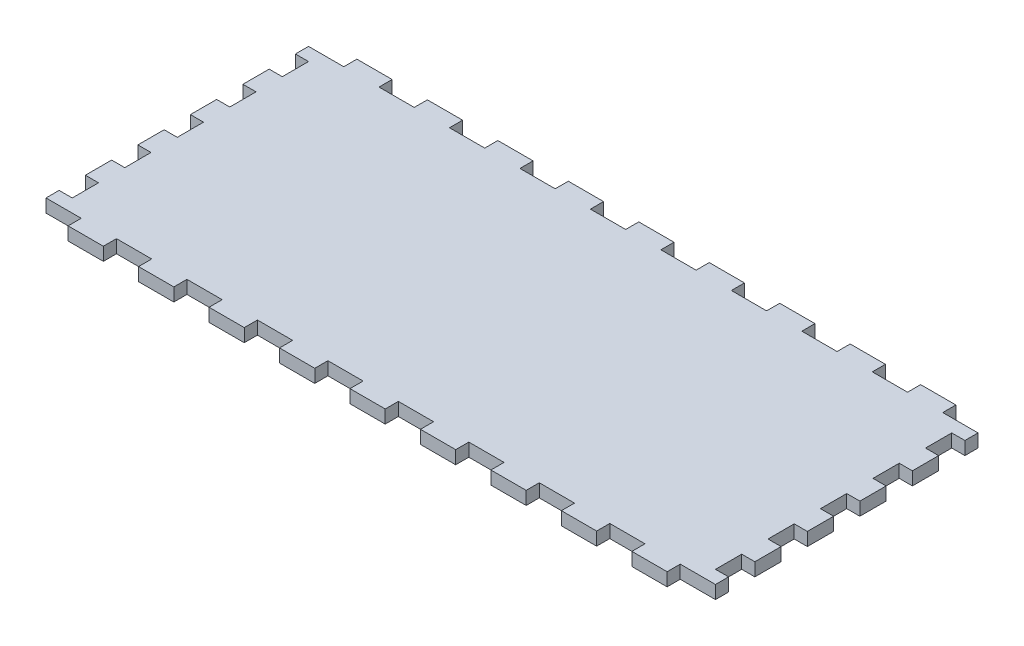
SolidWorks part; units mm, degrees
material "Acrylic (Medium-high impact)"
ref_plane "Front Plane" through (0, 0, 0) normal (0, 0, 1) x (1, 0, 0)
ref_plane "Top Plane" through (0, 0, 0) normal (0, 1, 0) x (1, 0, 0)
ref_plane "Right Plane" through (0, 0, 0) normal (1, 0, 0) x (0, 0, -1)
sketch "Sketch1" plane through (0, 0, 0) normal (0, 1, 0) x (1, 0, 0)
  line L1 (-161.925, 69.85) -> (161.925, 69.85)
  line L2 (-161.925, 69.85) -> (-161.925, -69.85)
  line L3 (-161.925, -69.85) -> (161.925, -69.85)
  line L4 (161.925, 69.85) -> (161.925, -69.85)
  point P4 (-161.925, 0)
  point P6 (0, 69.85)
  dimension "D1" = 139.7
  dimension "D2" = 323.85
extrude "Boss-Extrude1" add sketch "Sketch1" along normal blind 6.35
sketch "Sketch2" plane through (0, 6.35, 0) normal (0, 1, 0) x (1, 0, 0)
  line L0 (161.925, -69.85) -> (161.925, 69.85) construction
  line L1 (-161.925, 69.85) -> (161.925, 69.85)
  line L2 (-161.925, 69.85) -> (-161.925, -69.85)
  line L3 (-161.925, -69.85) -> (161.925, -69.85)
  line L4 (161.925, 69.85) -> (161.925, -69.85)
  line L5 (-161.925, -69.85) -> (161.925, -69.85) construction
  line L7 (-155.575, 63.5) -> (155.575, 63.5)
  line L8 (-155.575, 63.5) -> (-155.575, -63.5)
  line L9 (-155.575, -63.5) -> (155.575, -63.5)
  line L10 (155.575, 63.5) -> (155.575, -63.5)
  point P7 (-155.575, 0)
  point P14 (-161.925, 0)
  point P15 (0, -63.5)
  point P16 (0, -69.85)
  point P17 (155.575, 0)
  point P18 (161.925, 0)
  dimension "D1" = 6.35
  dimension "D2" = 6.35
extrude "Boss-Extrude2" add sketch "Sketch2" along normal blind 298.45
sketch "Sketch3" plane through (0, 0, 69.85) normal (0, 0, 1) x (1, 0, 0)
  line L0 (-50.673, 304.8) -> (-50.673, 0) construction
  line L2 (-155.575, 6.35) -> (155.575, 6.35) construction
  line L4 (-53.975, 283.21) -> (-53.975, 6.35)
  line L5 (-53.975, 6.35) -> (-47.371, 6.35)
  line L6 (-47.371, 292.354) -> (-47.371, 6.35)
  line L7 (-47.371, 292.354) -> (-66.929, 292.354)
  line L9 (-56.515, 285.75) -> (-66.929, 285.75)
  line L10 (-66.929, 292.354) -> (-66.929, 285.75)
  line L11 (-47.371, 101.6) -> (-34.671, 101.6) construction
  line L12 (-161.925, 0) -> (161.925, 0) construction
  line L13 (-37.846, 88.9) -> (-37.846, 101.6) construction
  line L14 (-41.021, 88.9) -> (-34.671, 88.9)
  line L15 (-41.021, 88.9) -> (-41.021, 71.9667)
  line L16 (-41.021, 71.9667) -> (-34.671, 71.9667)
  line L17 (-34.671, 88.9) -> (-34.671, 71.9667)
  line L18 (-41.021, 42.3333) -> (-34.671, 42.3333)
  line L19 (-41.021, 42.3333) -> (-41.021, 59.2667)
  line L20 (-41.021, 59.2667) -> (-34.671, 59.2667)
  line L21 (-34.671, 42.3333) -> (-34.671, 59.2667)
  line L26 (-41.021, 29.6333) -> (-34.671, 29.6333)
  line L27 (-41.021, 29.6333) -> (-41.021, 12.7)
  line L28 (-41.021, 12.7) -> (-34.671, 12.7)
  line L29 (-34.671, 29.6333) -> (-34.671, 12.7)
  line L30 (-37.846, 59.2667) -> (-37.846, 71.9667) construction
  line L31 (-37.846, 29.6333) -> (-37.846, 42.3333) construction
  line L32 (-37.846, 12.7) -> (-37.846, 0) construction
  line L33 (-161.925, 304.8) -> (161.925, 304.8) construction
  line L34 (-155.575, 304.8) -> (-155.575, 6.35) construction
  arc A0 (-53.975, 283.21) -> (-56.515, 285.75) centre (-56.515, 283.21) ccw
  point P5 (-50.673, 6.35)
  dimension "D5" = 2.54
  dimension "D1" = 6.604
  dimension "D2" = 12.954
  dimension "D3" = 6.604
  dimension "D4" = 286.004
  dimension "D6" = 101.6
  dimension "D7" = 12.7
  dimension "D8" = 12.7
  dimension "D9" = 6.35
  dimension "D10" = 101.6
extrude "Door Slot" cut sketch "Sketch3" against normal blind 12.7
sketch "Sketch4" plane through (0, 0, -63.5) normal (0, 0, 1) x (1, 0, 0)
  line L0 (-161.925, 304.8) -> (161.925, 304.8) construction
  line L1 (-73.279, 304.8) -> (-66.929, 304.8)
  line L2 (-73.279, 304.8) -> (-73.279, 6.35)
  line L3 (-73.279, 6.35) -> (-66.929, 6.35)
  line L4 (-66.929, 304.8) -> (-66.929, 6.35)
  line L5 (-44.196, 263.525) -> (-44.196, 247.65) construction
  line L6 (-66.929, 292.354) -> (-66.929, 285.75) construction
  line L7 (-47.371, 304.8) -> (-41.021, 304.8)
  line L8 (-47.371, 304.8) -> (-47.371, 6.35)
  line L9 (-47.371, 6.35) -> (-41.021, 6.35)
  line L10 (-41.021, 304.8) -> (-41.021, 6.35)
  line L11 (155.575, 6.35) -> (-155.575, 6.35) construction
  line L12 (-47.371, 6.35) -> (-47.371, 292.354) construction
  line L13 (-66.929, 304.8) -> (-73.279, 304.8)
  line L14 (-66.929, 304.8) -> (-66.929, 292.1)
  line L15 (-66.929, 292.1) -> (-73.279, 292.1)
  line L16 (-73.279, 304.8) -> (-73.279, 292.1)
  line L17 (-66.929, 276.225) -> (-73.279, 276.225)
  line L18 (-66.929, 276.225) -> (-66.929, 263.525)
  line L19 (-66.929, 263.525) -> (-73.279, 263.525)
  line L20 (-73.279, 276.225) -> (-73.279, 263.525)
  line L21 (-73.279, 6.35) -> (-66.929, 6.35)
  line L22 (-73.279, 6.35) -> (-73.279, 19.05)
  line L23 (-73.279, 19.05) -> (-66.929, 19.05)
  line L24 (-66.929, 6.35) -> (-66.929, 19.05)
  line L25 (-73.279, 34.925) -> (-66.929, 34.925)
  line L26 (-73.279, 34.925) -> (-73.279, 47.625)
  line L27 (-73.279, 47.625) -> (-66.929, 47.625)
  line L28 (-66.929, 34.925) -> (-66.929, 47.625)
  line L29 (-73.279, 92.075) -> (-66.929, 92.075)
  line L30 (-73.279, 92.075) -> (-73.279, 104.775)
  line L31 (-73.279, 104.775) -> (-66.929, 104.775)
  line L32 (-66.929, 92.075) -> (-66.929, 104.775)
  line L33 (-73.279, 149.225) -> (-66.929, 149.225)
  line L34 (-73.279, 149.225) -> (-73.279, 161.925)
  line L35 (-73.279, 161.925) -> (-66.929, 161.925)
  line L36 (-66.929, 149.225) -> (-66.929, 161.925)
  line L37 (-73.279, 177.8) -> (-66.929, 177.8)
  line L38 (-73.279, 177.8) -> (-73.279, 190.5)
  line L39 (-73.279, 190.5) -> (-66.929, 190.5)
  line L40 (-66.929, 177.8) -> (-66.929, 190.5)
  line L41 (-73.279, 206.375) -> (-66.929, 206.375)
  line L42 (-73.279, 206.375) -> (-73.279, 219.075)
  line L43 (-73.279, 219.075) -> (-66.929, 219.075)
  line L44 (-66.929, 206.375) -> (-66.929, 219.075)
  line L45 (-73.279, 234.95) -> (-66.929, 234.95)
  line L46 (-73.279, 234.95) -> (-73.279, 247.65)
  line L47 (-73.279, 247.65) -> (-66.929, 247.65)
  line L48 (-66.929, 234.95) -> (-66.929, 247.65)
  line L49 (-66.929, 133.35) -> (-73.279, 133.35)
  line L50 (-66.929, 133.35) -> (-66.929, 120.65)
  line L51 (-66.929, 120.65) -> (-73.279, 120.65)
  line L52 (-73.279, 133.35) -> (-73.279, 120.65)
  line L53 (-66.929, 76.2) -> (-73.279, 76.2)
  line L54 (-66.929, 76.2) -> (-66.929, 63.5)
  line L55 (-66.929, 63.5) -> (-73.279, 63.5)
  line L56 (-73.279, 76.2) -> (-73.279, 63.5)
  line L57 (-70.104, 304.8) -> (-70.104, 292.1) construction
  line L58 (-70.104, 292.1) -> (-70.104, 276.225) construction
  line L59 (-70.104, 276.225) -> (-70.104, 263.525) construction
  line L60 (-70.104, 247.65) -> (-70.104, 234.95) construction
  line L61 (-70.104, 234.95) -> (-70.104, 219.075) construction
  line L62 (-70.104, 219.075) -> (-70.104, 206.375) construction
  line L63 (-70.104, 206.375) -> (-70.104, 190.5) construction
  line L64 (-70.104, 190.5) -> (-70.104, 177.8) construction
  line L65 (-70.104, 177.8) -> (-70.104, 161.925) construction
  line L66 (-70.104, 161.925) -> (-70.104, 149.225) construction
  line L67 (-70.104, 133.35) -> (-70.104, 120.65) construction
  line L68 (-70.104, 120.65) -> (-70.104, 104.775) construction
  line L69 (-70.104, 104.775) -> (-70.104, 92.075) construction
  line L70 (-70.104, 92.075) -> (-70.104, 76.2) construction
  line L71 (-70.104, 76.2) -> (-70.104, 63.5) construction
  line L72 (-70.104, 63.5) -> (-70.104, 47.625) construction
  line L73 (-70.104, 47.625) -> (-70.104, 34.925) construction
  line L74 (-70.104, 34.925) -> (-70.104, 19.05) construction
  line L75 (-70.104, 19.05) -> (-70.104, 6.35) construction
  line L76 (-70.104, 149.225) -> (-70.104, 133.35) construction
  line L77 (-70.104, 263.525) -> (-70.104, 247.65) construction
  line L78 (-57.15, 304.8) -> (-57.15, 0) construction
  line L79 (161.925, 304.8) -> (-161.925, 304.8) construction
  line L80 (161.925, 0) -> (-161.925, 0) construction
  line L81 (-57.15, 8.3493) -> (-47.371, 8.3493) construction
  line L82 (-57.15, 8.3493) -> (-66.929, 8.3493) construction
  line L83 (-44.196, 149.225) -> (-44.196, 133.35) construction
  line L84 (-44.196, 19.05) -> (-44.196, 6.35) construction
  line L85 (-44.196, 34.925) -> (-44.196, 19.05) construction
  line L86 (-44.196, 47.625) -> (-44.196, 34.925) construction
  line L87 (-44.196, 63.5) -> (-44.196, 47.625) construction
  line L88 (-44.196, 76.2) -> (-44.196, 63.5) construction
  line L89 (-44.196, 92.075) -> (-44.196, 76.2) construction
  line L90 (-44.196, 104.775) -> (-44.196, 92.075) construction
  line L91 (-44.196, 120.65) -> (-44.196, 104.775) construction
  line L92 (-44.196, 133.35) -> (-44.196, 120.65) construction
  line L93 (-44.196, 161.925) -> (-44.196, 149.225) construction
  line L94 (-44.196, 177.8) -> (-44.196, 161.925) construction
  line L95 (-44.196, 190.5) -> (-44.196, 177.8) construction
  line L96 (-44.196, 206.375) -> (-44.196, 190.5) construction
  line L97 (-44.196, 219.075) -> (-44.196, 206.375) construction
  line L98 (-44.196, 234.95) -> (-44.196, 219.075) construction
  line L99 (-44.196, 247.65) -> (-44.196, 234.95) construction
  line L100 (-44.196, 276.225) -> (-44.196, 263.525) construction
  line L101 (-44.196, 292.1) -> (-44.196, 276.225) construction
  line L102 (-44.196, 304.8) -> (-44.196, 292.1) construction
  line L103 (-41.021, 76.2) -> (-41.021, 63.5)
  line L104 (-47.371, 63.5) -> (-41.021, 63.5)
  line L105 (-47.371, 76.2) -> (-47.371, 63.5)
  line L106 (-47.371, 76.2) -> (-41.021, 76.2)
  line L107 (-41.021, 133.35) -> (-41.021, 120.65)
  line L108 (-47.371, 120.65) -> (-41.021, 120.65)
  line L109 (-47.371, 133.35) -> (-47.371, 120.65)
  line L110 (-47.371, 133.35) -> (-41.021, 133.35)
  line L111 (-47.371, 234.95) -> (-47.371, 247.65)
  line L112 (-41.021, 247.65) -> (-47.371, 247.65)
  line L113 (-41.021, 234.95) -> (-41.021, 247.65)
  line L114 (-41.021, 234.95) -> (-47.371, 234.95)
  line L115 (-47.371, 206.375) -> (-47.371, 219.075)
  line L116 (-41.021, 219.075) -> (-47.371, 219.075)
  line L117 (-41.021, 206.375) -> (-41.021, 219.075)
  line L118 (-41.021, 206.375) -> (-47.371, 206.375)
  line L119 (-47.371, 177.8) -> (-47.371, 190.5)
  line L120 (-41.021, 190.5) -> (-47.371, 190.5)
  line L121 (-41.021, 177.8) -> (-41.021, 190.5)
  line L122 (-41.021, 177.8) -> (-47.371, 177.8)
  line L123 (-47.371, 149.225) -> (-47.371, 161.925)
  line L124 (-41.021, 161.925) -> (-47.371, 161.925)
  line L125 (-41.021, 149.225) -> (-41.021, 161.925)
  line L126 (-41.021, 149.225) -> (-47.371, 149.225)
  line L127 (-47.371, 92.075) -> (-47.371, 104.775)
  line L128 (-41.021, 104.775) -> (-47.371, 104.775)
  line L129 (-41.021, 92.075) -> (-41.021, 104.775)
  line L130 (-41.021, 92.075) -> (-47.371, 92.075)
  line L131 (-47.371, 34.925) -> (-47.371, 47.625)
  line L132 (-41.021, 47.625) -> (-47.371, 47.625)
  line L133 (-41.021, 34.925) -> (-41.021, 47.625)
  line L134 (-41.021, 34.925) -> (-47.371, 34.925)
  line L135 (-47.371, 6.35) -> (-47.371, 19.05)
  line L136 (-41.021, 19.05) -> (-47.371, 19.05)
  line L137 (-41.021, 6.35) -> (-41.021, 19.05)
  line L138 (-41.021, 6.35) -> (-47.371, 6.35)
  line L139 (-41.021, 276.225) -> (-41.021, 263.525)
  line L140 (-47.371, 263.525) -> (-41.021, 263.525)
  line L141 (-47.371, 276.225) -> (-47.371, 263.525)
  line L142 (-47.371, 276.225) -> (-41.021, 276.225)
  line L143 (-41.021, 304.8) -> (-41.021, 292.1)
  line L144 (-47.371, 292.1) -> (-41.021, 292.1)
  line L145 (-47.371, 304.8) -> (-47.371, 292.1)
  line L146 (-47.371, 304.8) -> (-41.021, 304.8)
  line L147 (-47.371, 304.8) -> (-47.371, 6.35)
  line L148 (-41.021, 6.35) -> (-47.371, 6.35)
  line L149 (-41.021, 304.8) -> (-41.021, 6.35)
  line L150 (-41.021, 304.8) -> (-47.371, 304.8)
  point P14 (-66.929, 289.052)
  dimension "D1" = 6.35
  dimension "D2" = 12.7
extrude "Door Guide Holes" cut sketch "Sketch4" against normal up to next (6.35 mm away) contours L17 L4 L15 L2 | L2 L47 L4 L19 | L45 L2 L43 L4 | L41 L2 L39 L4 | L37 L2 L35 L4 | L49 L4 L33 L2 | L4 L51 L2 L31 | L53 L4 L29 L2 | L4 L55 L2 L27 | L25 L2 L23 L4
ref_plane "Plane1" through (-57.15, 0, 0) normal (-1, 0, 0) x (0, 0, 1)
mirror "Mirror1" about plane through (-57.15, 0, 0) normal (-1, 0, 0) of "Door Guide Holes"
sketch "Lever Holes" plane through (0, 0, 69.85) normal (0, 0, 1) x (1, 0, 0)
  line L0 (49.276, 31.75) -> (58.928, 31.75)
  line L1 (49.276, 31.75) -> (49.276, 25.4)
  line L2 (49.276, 25.4) -> (58.928, 25.4)
  line L3 (58.928, 31.75) -> (58.928, 25.4)
  line L4 (36.1315, 19.05) -> (42.4815, 19.05)
  line L5 (36.1315, 19.05) -> (36.1315, 12.7)
  line L6 (36.1315, 12.7) -> (42.4815, 12.7)
  line L7 (42.4815, 19.05) -> (42.4815, 12.7)
  line L8 (65.7225, 19.05) -> (72.0725, 19.05)
  line L9 (65.7225, 19.05) -> (65.7225, 12.7)
  line L10 (65.7225, 12.7) -> (72.0725, 12.7)
  line L11 (72.0725, 19.05) -> (72.0725, 12.7)
  line L12 (42.4815, 15.875) -> (65.7225, 15.875) construction
  line L13 (-161.925, 0) -> (161.925, 0) construction
  line L14 (-47.371, 6.35) -> (155.575, 6.35) construction
  line L15 (155.575, 6.35) -> (-155.575, 6.35) construction
  point P12 (54.102, 15.875)
  point P13 (54.102, 25.4)
  point P24 (54.102, 6.35)
  dimension "D1" = 9.652
  dimension "D2" = 6.35
  dimension "D3" = 6.35
  dimension "D4" = 6.35
  dimension "D5" = 23.241
  dimension "D6" = 25.4
  dimension "D7" = 12.7
extrude "Cut-Extrude1" cut sketch "Lever Holes" against normal through all
sketch "Sketch7" plane through (161.925, 0, 0) normal (1, 0, 0) x (0, 0, -1)
  line L0 (-37.211, 92.583) -> (37.211, 92.583)
  line L1 (-37.211, 92.583) -> (-37.211, 18.161)
  line L2 (-37.211, 18.161) -> (37.211, 18.161)
  line L3 (37.211, 92.583) -> (37.211, 18.161)
  line L4 (-69.85, 0) -> (69.85, 0) construction
  circle A0 centre (0, 55.372) radius 26.9875
  circle A1 centre (-37.211, 92.583) radius 3.175
  circle A2 centre (37.211, 92.583) radius 3.175
  circle A3 centre (-37.211, 18.161) radius 3.175
  circle A4 centre (37.211, 18.161) radius 3.175
  point P9 (0, 18.161)
  point P10 (-37.211, 55.372)
  dimension "D3" = 53.975
  dimension "D4" = 6.35
  dimension "D1" = 74.422
  dimension "D2" = 55.372
extrude "Cut-Extrude2" cut sketch "Sketch7" against normal up to next contours A0 | L0 A1 L1 | L1 A1 L0 | L3 A2 L0 | L0 A2 L3 | L2 A3 L1 | L1 A3 L2 | L2 A4 L3 | L3 A4 L2
sketch "Sketch8" plane through (-161.925, 0, 0) normal (-1, 0, 0) x (0, 0, 1)
  line L0 (-69.85, 0) -> (69.85, 0) construction
  circle A0 centre (0, 19.05) radius 3.175
  point P6 (0, 0)
  dimension "D1" = 6.35
  dimension "D2" = 19.05
extrude "Cut-Extrude3" cut sketch "Sketch8" against normal up to next
sketch "Sketch10" plane through (0, 0, 0) normal (0, -1, 0) x (1, 0, 0)
  line L0 (-155.575, 63.5) -> (155.575, 63.5) construction
  line L1 (-161.925, 69.85) -> (-144.8803, 69.85)
  line L2 (-161.925, 69.85) -> (-161.925, 63.5)
  line L3 (-161.925, 63.5) -> (-144.8803, 63.5)
  line L4 (-144.8803, 69.85) -> (-144.8803, 63.5)
  line L5 (-144.8803, 69.85) -> (-127.8355, 69.85)
  line L6 (-144.8803, 69.85) -> (-144.8803, 63.5)
  line L7 (-144.8803, 63.5) -> (-127.8355, 63.5)
  line L8 (-127.8355, 69.85) -> (-127.8355, 63.5)
  line L9 (-127.8355, 69.85) -> (-110.7908, 69.85)
  line L10 (-127.8355, 69.85) -> (-127.8355, 63.5)
  line L11 (-127.8355, 63.5) -> (-110.7908, 63.5)
  line L12 (-110.7908, 69.85) -> (-110.7908, 63.5)
  line L13 (-110.7908, 69.85) -> (-93.7461, 69.85)
  line L14 (-110.7908, 69.85) -> (-110.7908, 63.5)
  line L15 (-110.7908, 63.5) -> (-93.7461, 63.5)
  line L16 (-93.7461, 69.85) -> (-93.7461, 63.5)
  line L17 (-161.925, 69.85) -> (161.925, 69.85) construction
  line L18 (-66.929, 63.5) -> (-47.371, 63.5) construction
  line L19 (-93.7461, 69.85) -> (-76.7013, 69.85)
  line L20 (-93.7461, 69.85) -> (-93.7461, 63.5)
  line L21 (-93.7461, 63.5) -> (-76.7013, 63.5)
  line L22 (-76.7013, 69.85) -> (-76.7013, 63.5)
  line L23 (-76.7013, 69.85) -> (-59.6566, 69.85)
  line L24 (-76.7013, 69.85) -> (-76.7013, 63.5)
  line L25 (-76.7013, 63.5) -> (-59.6566, 63.5)
  line L26 (-59.6566, 69.85) -> (-59.6566, 63.5)
  line L27 (-59.6566, 69.85) -> (-42.6118, 69.85)
  line L28 (-59.6566, 69.85) -> (-59.6566, 63.5)
  line L29 (-59.6566, 63.5) -> (-42.6118, 63.5)
  line L30 (-42.6118, 69.85) -> (-42.6118, 63.5)
  line L31 (-42.6118, 69.85) -> (-25.5671, 69.85)
  line L32 (-42.6118, 69.85) -> (-42.6118, 63.5)
  line L33 (-42.6118, 63.5) -> (-25.5671, 63.5)
  line L34 (-25.5671, 69.85) -> (-25.5671, 63.5)
  line L36 (-25.5671, 69.85) -> (-8.5224, 69.85)
  line L37 (-25.5671, 69.85) -> (-25.5671, 63.5)
  line L38 (-25.5671, 63.5) -> (-8.5224, 63.5)
  line L39 (-8.5224, 69.85) -> (-8.5224, 63.5)
  line L40 (-8.5224, 69.85) -> (8.5224, 69.85)
  line L41 (-8.5224, 69.85) -> (-8.5224, 63.5)
  line L42 (-8.5224, 63.5) -> (8.5224, 63.5)
  line L43 (8.5224, 69.85) -> (8.5224, 63.5)
  line L44 (8.5224, 69.85) -> (25.5671, 69.85)
  line L45 (8.5224, 69.85) -> (8.5224, 63.5)
  line L46 (8.5224, 63.5) -> (25.5671, 63.5)
  line L47 (25.5671, 69.85) -> (25.5671, 63.5)
  line L48 (25.5671, 69.85) -> (42.6118, 69.85)
  line L49 (25.5671, 69.85) -> (25.5671, 63.5)
  line L50 (25.5671, 63.5) -> (42.6118, 63.5)
  line L51 (42.6118, 69.85) -> (42.6118, 63.5)
  line L52 (42.6118, 69.85) -> (59.6566, 69.85)
  line L53 (42.6118, 69.85) -> (42.6118, 63.5)
  line L54 (42.6118, 63.5) -> (59.6566, 63.5)
  line L55 (59.6566, 69.85) -> (59.6566, 63.5)
  line L56 (59.6566, 69.85) -> (76.7013, 69.85)
  line L57 (59.6566, 69.85) -> (59.6566, 63.5)
  line L58 (59.6566, 63.5) -> (76.7013, 63.5)
  line L59 (76.7013, 69.85) -> (76.7013, 63.5)
  line L60 (76.7013, 69.85) -> (93.7461, 69.85)
  line L61 (76.7013, 69.85) -> (76.7013, 63.5)
  line L62 (76.7013, 63.5) -> (93.7461, 63.5)
  line L63 (93.7461, 69.85) -> (93.7461, 63.5)
  line L64 (93.7461, 69.85) -> (110.7908, 69.85)
  line L65 (93.7461, 69.85) -> (93.7461, 63.5)
  line L66 (93.7461, 63.5) -> (110.7908, 63.5)
  line L67 (110.7908, 69.85) -> (110.7908, 63.5)
  line L68 (110.7908, 69.85) -> (127.8355, 69.85)
  line L69 (110.7908, 69.85) -> (110.7908, 63.5)
  line L70 (110.7908, 63.5) -> (127.8355, 63.5)
  line L71 (127.8355, 69.85) -> (127.8355, 63.5)
  line L72 (127.8355, 69.85) -> (144.8803, 69.85)
  line L73 (127.8355, 69.85) -> (127.8355, 63.5)
  line L74 (127.8355, 63.5) -> (144.8803, 63.5)
  line L75 (144.8803, 69.85) -> (144.8803, 63.5)
  line L76 (-155.575, -63.5) -> (-155.575, 63.5) construction
  line L77 (-161.925, 69.85) -> (-155.575, 69.85)
  line L78 (-161.925, 69.85) -> (-161.925, 57.15)
  line L79 (-161.925, 57.15) -> (-155.575, 57.15)
  line L80 (-155.575, 69.85) -> (-155.575, 57.15)
  line L82 (-161.925, 57.15) -> (-155.575, 57.15)
  line L83 (-161.925, 57.15) -> (-161.925, 44.45)
  line L84 (-161.925, 44.45) -> (-155.575, 44.45)
  line L85 (-155.575, 57.15) -> (-155.575, 44.45)
  line L86 (-161.925, 44.45) -> (-155.575, 44.45)
  line L87 (-161.925, 44.45) -> (-161.925, 31.75)
  line L88 (-161.925, 31.75) -> (-155.575, 31.75)
  line L89 (-155.575, 44.45) -> (-155.575, 31.75)
  line L90 (-161.925, 31.75) -> (-155.575, 31.75)
  line L91 (-161.925, 31.75) -> (-161.925, 19.05)
  line L92 (-161.925, 19.05) -> (-155.575, 19.05)
  line L93 (-155.575, 31.75) -> (-155.575, 19.05)
  line L94 (-161.925, 19.05) -> (-155.575, 19.05)
  line L95 (-161.925, 19.05) -> (-161.925, 6.35)
  line L96 (-161.925, 6.35) -> (-155.575, 6.35)
  line L97 (-155.575, 19.05) -> (-155.575, 6.35)
  line L98 (-161.925, 6.35) -> (-155.575, 6.35)
  line L99 (-161.925, 6.35) -> (-161.925, -6.35)
  line L100 (-161.925, -6.35) -> (-155.575, -6.35)
  line L101 (-155.575, 6.35) -> (-155.575, -6.35)
  line L102 (-161.925, -6.35) -> (-155.575, -6.35)
  line L103 (-161.925, -6.35) -> (-161.925, -19.05)
  line L104 (-161.925, -19.05) -> (-155.575, -19.05)
  line L105 (-155.575, -6.35) -> (-155.575, -19.05)
  line L106 (-161.925, -19.05) -> (-155.575, -19.05)
  line L107 (-161.925, -19.05) -> (-161.925, -31.75)
  line L108 (-161.925, -31.75) -> (-155.575, -31.75)
  line L109 (-155.575, -19.05) -> (-155.575, -31.75)
  line L110 (-161.925, -31.75) -> (-155.575, -31.75)
  line L111 (-161.925, -31.75) -> (-161.925, -44.45)
  line L112 (-161.925, -44.45) -> (-155.575, -44.45)
  line L113 (-155.575, -31.75) -> (-155.575, -44.45)
  line L114 (-161.925, -44.45) -> (-155.575, -44.45)
  line L115 (-161.925, -44.45) -> (-161.925, -57.15)
  line L116 (-161.925, -57.15) -> (-155.575, -57.15)
  line L117 (-155.575, -44.45) -> (-155.575, -57.15)
  line L118 (161.925, 69.85) -> (161.925, -69.85) construction
  line L119 (144.8803, 69.85) -> (161.925, 69.85)
  line L120 (144.8803, 69.85) -> (144.8803, 63.5)
  line L121 (144.8803, 63.5) -> (161.925, 63.5)
  line L122 (161.925, 69.85) -> (161.925, 63.5)
  line L123 (161.925, -69.85) -> (-161.925, -69.85) construction
  line L124 (-161.925, -57.15) -> (-155.575, -57.15)
  line L125 (-161.925, -57.15) -> (-161.925, -69.85)
  line L126 (-161.925, -69.85) -> (-155.575, -69.85)
  line L127 (-155.575, -57.15) -> (-155.575, -69.85)
  line L128 (55, 0) -> (-55, 0) construction
  line L129 (161.925, -69.85) -> (161.925, -63.5)
  line L130 (144.8803, -63.5) -> (161.925, -63.5)
  line L131 (144.8803, -69.85) -> (161.925, -69.85)
  line L132 (144.8803, -69.85) -> (144.8803, -63.5)
  line L133 (127.8355, -63.5) -> (144.8803, -63.5)
  line L134 (127.8355, -69.85) -> (144.8803, -69.85)
  line L135 (127.8355, -69.85) -> (127.8355, -63.5)
  line L136 (110.7908, -63.5) -> (127.8355, -63.5)
  line L137 (110.7908, -69.85) -> (127.8355, -69.85)
  line L138 (110.7908, -69.85) -> (110.7908, -63.5)
  line L139 (93.7461, -63.5) -> (110.7908, -63.5)
  line L140 (93.7461, -69.85) -> (110.7908, -69.85)
  line L141 (93.7461, -69.85) -> (93.7461, -63.5)
  line L142 (76.7013, -63.5) -> (93.7461, -63.5)
  line L143 (76.7013, -69.85) -> (93.7461, -69.85)
  line L144 (59.6566, -63.5) -> (76.7013, -63.5)
  line L145 (76.7013, -69.85) -> (76.7013, -63.5)
  line L146 (59.6566, -69.85) -> (76.7013, -69.85)
  line L147 (59.6566, -69.85) -> (59.6566, -63.5)
  line L148 (42.6118, -63.5) -> (59.6566, -63.5)
  line L149 (42.6118, -69.85) -> (59.6566, -69.85)
  line L150 (42.6118, -69.85) -> (42.6118, -63.5)
  line L151 (25.5671, -63.5) -> (42.6118, -63.5)
  line L152 (25.5671, -69.85) -> (42.6118, -69.85)
  line L153 (25.5671, -69.85) -> (25.5671, -63.5)
  line L154 (8.5224, -69.85) -> (25.5671, -69.85)
  line L155 (8.5224, -63.5) -> (25.5671, -63.5)
  line L156 (8.5224, -69.85) -> (8.5224, -63.5)
  line L157 (-8.5224, -63.5) -> (8.5224, -63.5)
  line L158 (-8.5224, -69.85) -> (8.5224, -69.85)
  line L159 (-25.5671, -63.5) -> (-8.5224, -63.5)
  line L160 (-8.5224, -69.85) -> (-8.5224, -63.5)
  line L161 (-25.5671, -69.85) -> (-8.5224, -69.85)
  line L162 (-25.5671, -69.85) -> (-25.5671, -63.5)
  line L163 (-42.6118, -63.5) -> (-25.5671, -63.5)
  line L164 (-42.6118, -69.85) -> (-25.5671, -69.85)
  line L165 (-42.6118, -69.85) -> (-42.6118, -63.5)
  line L166 (-59.6566, -63.5) -> (-42.6118, -63.5)
  line L167 (-59.6566, -69.85) -> (-42.6118, -69.85)
  line L168 (-59.6566, -69.85) -> (-59.6566, -63.5)
  line L169 (-76.7013, -69.85) -> (-59.6566, -69.85)
  line L170 (-76.7013, -63.5) -> (-59.6566, -63.5)
  line L171 (-93.7461, -63.5) -> (-76.7013, -63.5)
  line L172 (-76.7013, -69.85) -> (-76.7013, -63.5)
  line L173 (-93.7461, -69.85) -> (-76.7013, -69.85)
  line L174 (-110.7908, -69.85) -> (-93.7461, -69.85)
  line L175 (-110.7908, -63.5) -> (-93.7461, -63.5)
  line L176 (-93.7461, -69.85) -> (-93.7461, -63.5)
  line L177 (-127.8355, -69.85) -> (-127.8355, -63.5)
  line L178 (-127.8355, -69.85) -> (-110.7908, -69.85)
  line L179 (-110.7908, -69.85) -> (-110.7908, -63.5)
  line L180 (-127.8355, -63.5) -> (-110.7908, -63.5)
  line L181 (-144.8803, -63.5) -> (-127.8355, -63.5)
  line L182 (-144.8803, -69.85) -> (-127.8355, -69.85)
  line L183 (-144.8803, -69.85) -> (-144.8803, -63.5)
  line L184 (-161.925, -69.85) -> (-144.8803, -69.85)
  line L185 (-161.925, -69.85) -> (-161.925, -63.5)
  line L186 (-161.925, -63.5) -> (-144.8803, -63.5)
  line L187 (0, -55) -> (0, 55) construction
  line L188 (161.925, -69.85) -> (155.575, -69.85)
  line L189 (155.575, -57.15) -> (155.575, -69.85)
  line L190 (161.925, -57.15) -> (161.925, -69.85)
  line L191 (161.925, -57.15) -> (155.575, -57.15)
  line L192 (155.575, -44.45) -> (155.575, -57.15)
  line L193 (161.925, -44.45) -> (161.925, -57.15)
  line L194 (161.925, -44.45) -> (155.575, -44.45)
  line L195 (155.575, -31.75) -> (155.575, -44.45)
  line L196 (161.925, -31.75) -> (161.925, -44.45)
  line L197 (161.925, -31.75) -> (155.575, -31.75)
  line L198 (161.925, -19.05) -> (161.925, -31.75)
  line L199 (155.575, -19.05) -> (155.575, -31.75)
  line L200 (155.575, -6.35) -> (155.575, -19.05)
  line L201 (161.925, -6.35) -> (161.925, -19.05)
  line L202 (161.925, -19.05) -> (155.575, -19.05)
  line L203 (161.925, -6.35) -> (155.575, -6.35)
  line L204 (155.575, 6.35) -> (155.575, -6.35)
  line L205 (161.925, 6.35) -> (161.925, -6.35)
  line L206 (161.925, 6.35) -> (155.575, 6.35)
  line L207 (155.575, 19.05) -> (155.575, 6.35)
  line L208 (161.925, 19.05) -> (161.925, 6.35)
  line L209 (161.925, 19.05) -> (155.575, 19.05)
  line L210 (161.925, 31.75) -> (155.575, 31.75)
  line L211 (161.925, 44.45) -> (155.575, 44.45)
  line L212 (161.925, 57.15) -> (155.575, 57.15)
  line L213 (155.575, 31.75) -> (155.575, 19.05)
  line L214 (161.925, 31.75) -> (161.925, 19.05)
  line L215 (155.575, 44.45) -> (155.575, 31.75)
  line L216 (161.925, 44.45) -> (161.925, 31.75)
  line L217 (155.575, 57.15) -> (155.575, 44.45)
  line L218 (161.925, 57.15) -> (161.925, 44.45)
  line L219 (155.575, 69.85) -> (155.575, 57.15)
  line L220 (161.925, 69.85) -> (161.925, 57.15)
  line M28 (-161.925, 69.85) -> (-161.925, -69.85)
  line M29 (-161.925, -69.85) -> (161.925, -69.85)
  line M30 (161.925, -69.85) -> (161.925, 69.85)
  line M31 (161.925, 69.85) -> (-161.925, 69.85)
sketch "Sketch9" plane through (0, 0, -69.85) normal (0, 0, -1) x (-1, 0, 0)
  line L0 (161.925, 304.8) -> (161.925, 0) construction
  line L1 (-161.925, 304.8) -> (161.925, 304.8)
  line L2 (-161.925, 304.8) -> (-161.925, 6.35)
  line L3 (-161.925, 6.35) -> (161.925, 6.35)
  line L4 (161.925, 304.8) -> (161.925, 6.35)
  line L5 (-155.575, 6.35) -> (155.575, 6.35) construction
extrude "Cut-Extrude4" cut sketch "Sketch9" against normal through all
extrude "Cut-Extrude6" cut sketch "Sketch10" against normal through all contours L80 L3 L4 M31 | L80 L1 L3 M28 | L12 L8 L11 M31 | L22 L16 L21 M31 | L30 L26 L29 M31 | L39 L34 L38 M31 | L47 L43 L46 M31 | L55 L51 L54 M31 | L63 L59 L62 M31 | L71 L67 L70 M31 | L219 L119 L75 L121 | L219 L121 M31 M30 | L212 L217 L211 M30 | L210 L213 L209 M30 | L206 L204 L203 M30 | L202 L199 L197 M30 | L194 L192 L191 M30 | L130 L189 L131 M30 | L189 L130 L132 M29 | L138 L135 L136 M29 | L145 L141 L142 M29 | L150 L147 L148 M29 | L156 L153 L155 M29 | L162 L160 L159 M29 | L168 L165 L166 M29 | L176 L172 L171 M29 | L180 L177 L179 M29 | L186 L125 L127 M29 | L186 L127 L183 M29 | L117 L112 L116 M28 | L109 L104 L108 M28 | L101 L96 L100 M28 | L93 L88 L92 M28 | L85 L79 L84 M28
